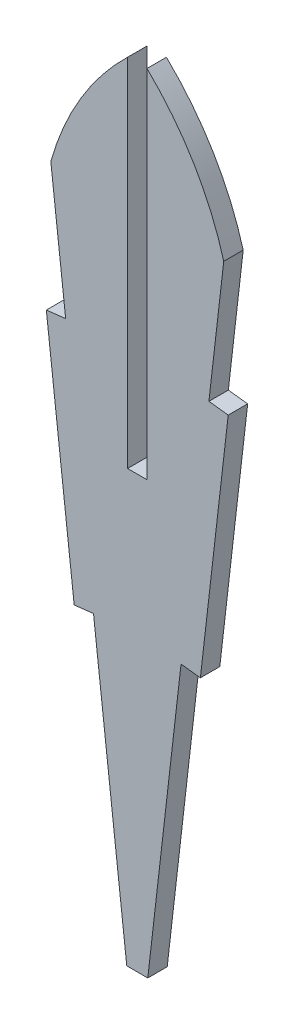
SolidWorks part; units mm, degrees
ref_plane "Front Plane" through (0, 0, 0) normal (0, 0, 1) x (1, 0, 0)
ref_plane "Top Plane" through (0, 0, 0) normal (0, 1, 0) x (1, 0, 0)
ref_plane "Right Plane" through (0, 0, 0) normal (1, 0, 0) x (0, 0, -1)
sketch "Sketch1" plane through (0, 0, 0) normal (0, 0, 1) x (1, 0, 0)
  line L0 (0, -185.0621) -> (-1.524, -185.0621)
  line L1 (6.3647, -177.4915) -> (4.1821, -196.416)
  line L2 (-1.524, -185.0621) -> (-1.524, -157.1523)
  line L3 (2.6681, -196.2414) -> (4.1821, -196.416)
  line L4 (-7.5376, -167.2346) -> (-6.3747, -177.3168)
  line L5 (-4.1921, -196.2414) -> (-1.5851, -218.846)
  line L6 (-6.3747, -177.3168) -> (-7.8887, -177.4915)
  line L7 (-4.1921, -196.2414) -> (-5.7061, -196.416)
  line L8 (-0.762, -185.0621) -> (-0.762, -247.1656) construction
  line L9 (-7.8887, -177.4915) -> (-5.7061, -196.416)
  line L10 (-1.5851, -218.846) -> (0.0611, -218.846)
  line L11 (4.8507, -177.3168) -> (6.3647, -177.4915)
  line L12 (2.6681, -196.2414) -> (0.0611, -218.846)
  line L13 (6.0136, -167.2346) -> (4.8507, -177.3168)
  line L14 (0, -185.0621) -> (0, -157.1523)
  arc A0 (-7.5376, -167.2346) -> (-1.524, -157.1523) centre (14.0358, -173.2675) cw
  arc A1 (6.0136, -167.2346) -> (0, -157.1523) centre (-15.5598, -173.2675) ccw
  point P21 (-0.762, -219.2285)
  point P26 (-0.762, -185.0621)
extrude "Boss-Extrude1" add sketch "Sketch1" along normal blind 1.524
